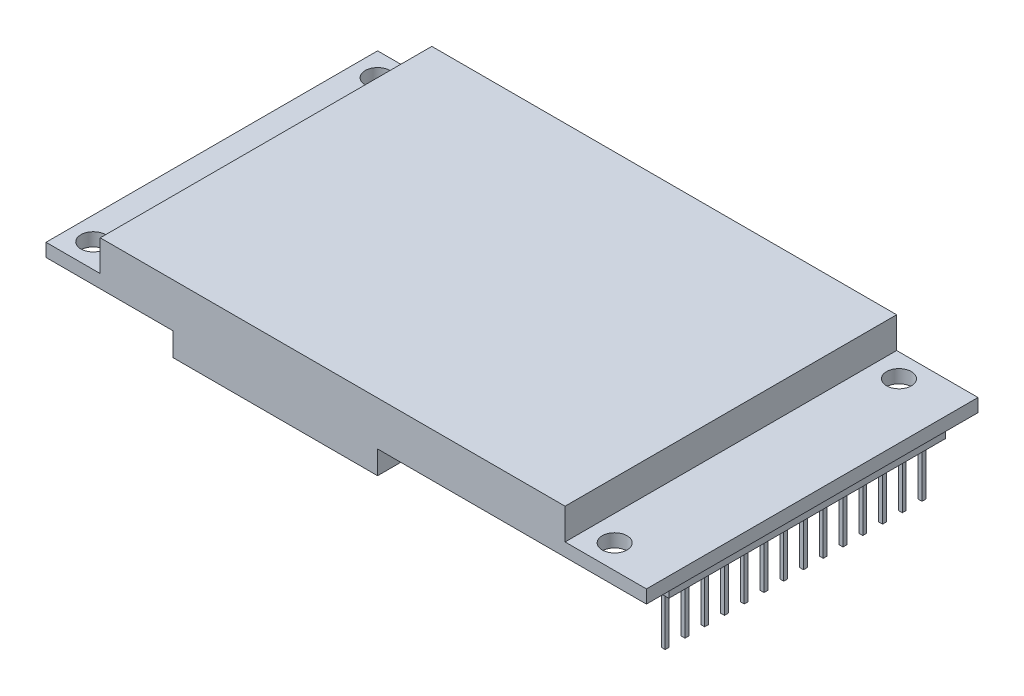
SolidWorks part; units mm, degrees
ref_plane "Płaszczyzna przednia" through (0, 0, 0) normal (0, 0, 1) x (1, 0, 0)
ref_plane "Płaszczyzna górna" through (0, 0, 0) normal (0, 1, 0) x (1, 0, 0)
ref_plane "Płaszczyzna prawa" through (0, 0, 0) normal (1, 0, 0) x (0, 0, -1)
sketch "Szkic1" plane through (0, 0, 0) normal (0, 1, 0) x (1, 0, 0)
  line L1 (-38.75, -21.4) -> (38.75, -21.4)
  line L2 (-38.75, -21.4) -> (-38.75, 21.4)
  line L3 (-38.75, 21.4) -> (38.75, 21.4)
  line L4 (38.75, -21.4) -> (38.75, 21.4)
  line L5 (-38.75, -21.4) -> (38.75, 21.4) construction
  line L6 (-38.75, 21.4) -> (38.75, -21.4) construction
  circle A0 centre (-35.75, 18.4) radius 1.6
  circle A2 centre (31.55, 18.4) radius 1.6
  circle A3 centre (31.55, -18.3) radius 1.6
  circle A4 centre (-35.75, -18.3) radius 1.6
  point P0 (0, 0)
  point P8 (0, 0)
  point P9 (0, 0)
  point P10 (0, 0)
  dimension "D3" = 3.2
  dimension "D8" = 36.7
  dimension "D10" = 67.3
  dimension "D1" = 42.8
  dimension "D2" = 77.5
  dimension "D6" = 3
  dimension "D7" = 3
  dimension "D4" = 2
  dimension "D5" = 2
extrude "Dodanie-wyciągnięcie1" add sketch "Szkic1" along normal blind 1.7
sketch "Szkic2" plane through (0, 1.7, 0) normal (0, 1, 0) x (1, 0, 0)
  line L0 (-38.75, -21.4) -> (38.75, -21.4) construction
  line L1 (-31.75, -21.4) -> (28.25, -21.4)
  line L2 (-31.75, -21.4) -> (-31.75, 21.4)
  line L3 (-31.75, 21.4) -> (28.25, 21.4)
  line L4 (28.25, -21.4) -> (28.25, 21.4)
  line L5 (38.75, 21.4) -> (-38.75, 21.4) construction
  line L6 (-38.75, 21.4) -> (-38.75, -21.4) construction
  dimension "D1" = 60
  dimension "D2" = 7
extrude "Dodanie-wyciągnięcie2" add sketch "Szkic2" along normal blind 4
sketch "Szkic3" plane through (0, 0, 0) normal (0, -1, 0) x (1, 0, 0)
  line L0 (4.05, 21.4) -> (4.05, 4.5)
  line L1 (-38.75, 21.4) -> (38.75, 21.4) construction
  line L2 (4.05, 4.5) -> (-20.45, 4.5)
  line L3 (-20.45, 4.5) -> (-20.45, 9.5)
  line L4 (-20.45, 9.5) -> (-22.35, 12.4)
  line L5 (-22.35, 12.4) -> (-22.35, 21.4)
  line L6 (-22.35, 21.4) -> (4.05, 21.4)
  line L7 (-38.75, -21.4) -> (-38.75, 21.4) construction
  point P2 (0, 0)
  dimension "D1" = 16.9
  dimension "D2" = 26.4
  dimension "D3" = 24.5
  dimension "D4" = 5
  dimension "D5" = 9
  dimension "D6" = 16.4
extrude "Dodanie-wyciągnięcie3" add sketch "Szkic3" along normal blind 3
sketch "Szkic4" plane through (0, 0, 0) normal (0, -1, 0) x (1, 0, 0)
  line L0 (38.75, 21.4) -> (38.75, -21.4) construction
  line L1 (34.55, -17.9) -> (38.05, -17.9)
  line L2 (34.55, -17.9) -> (34.55, 17.8)
  line L3 (34.55, 17.8) -> (38.05, 17.8)
  line L4 (38.05, -17.9) -> (38.05, 17.8)
  line L5 (38.75, -21.4) -> (-38.75, -21.4) construction
  dimension "D1" = 35.7
  dimension "D2" = 3.5
  dimension "D3" = 0.7
  dimension "D4" = 3.5
extrude "Dodanie-wyciągnięcie4" add sketch "Szkic4" along normal blind 8.5
sketch "Szkic5" plane through (0, -8.5, 0) normal (0, -1, 0) x (1, 0, 0)
  line L0 (36.3, 17.8) -> (36.3, -17.9) construction
  line L1 (36.05, 16.775) -> (36.55, 16.775)
  line L2 (36.05, 16.775) -> (36.05, 16.275)
  line L3 (36.05, 16.275) -> (36.55, 16.275)
  line L4 (36.55, 16.775) -> (36.55, 16.275)
  line L5 (38.05, 17.8) -> (34.55, 17.8) construction
  line L6 (34.55, -17.9) -> (38.05, -17.9) construction
  line L7 (36.55, 14.225) -> (36.55, 13.725)
  line L8 (36.05, 13.725) -> (36.55, 13.725)
  line L9 (36.05, 14.225) -> (36.05, 13.725)
  line L10 (36.05, 14.225) -> (36.55, 14.225)
  line L11 (36.55, 11.675) -> (36.55, 11.175)
  line L12 (36.05, 11.175) -> (36.55, 11.175)
  line L13 (36.05, 11.675) -> (36.05, 11.175)
  line L14 (36.05, 11.675) -> (36.55, 11.675)
  line L15 (36.55, 9.125) -> (36.55, 8.625)
  line L16 (36.05, 8.625) -> (36.55, 8.625)
  line L17 (36.05, 9.125) -> (36.05, 8.625)
  line L18 (36.05, 9.125) -> (36.55, 9.125)
  line L19 (36.55, 6.575) -> (36.55, 6.075)
  line L20 (36.05, 6.075) -> (36.55, 6.075)
  line L21 (36.05, 6.575) -> (36.05, 6.075)
  line L22 (36.05, 6.575) -> (36.55, 6.575)
  line L23 (36.55, 4.025) -> (36.55, 3.525)
  line L24 (36.05, 3.525) -> (36.55, 3.525)
  line L25 (36.05, 4.025) -> (36.05, 3.525)
  line L26 (36.05, 4.025) -> (36.55, 4.025)
  line L27 (36.55, 1.475) -> (36.55, 0.975)
  line L28 (36.05, 0.975) -> (36.55, 0.975)
  line L29 (36.05, 1.475) -> (36.05, 0.975)
  line L30 (36.05, 1.475) -> (36.55, 1.475)
  line L31 (36.55, -1.075) -> (36.55, -1.575)
  line L32 (36.05, -1.575) -> (36.55, -1.575)
  line L33 (36.05, -1.075) -> (36.05, -1.575)
  line L34 (36.05, -1.075) -> (36.55, -1.075)
  line L35 (36.55, -3.625) -> (36.55, -4.125)
  line L36 (36.05, -4.125) -> (36.55, -4.125)
  line L37 (36.05, -3.625) -> (36.05, -4.125)
  line L38 (36.05, -3.625) -> (36.55, -3.625)
  line L39 (36.55, -6.175) -> (36.55, -6.675)
  line L40 (36.05, -6.675) -> (36.55, -6.675)
  line L41 (36.05, -6.175) -> (36.05, -6.675)
  line L42 (36.05, -6.175) -> (36.55, -6.175)
  line L43 (36.55, -8.725) -> (36.55, -9.225)
  line L44 (36.05, -9.225) -> (36.55, -9.225)
  line L45 (36.05, -8.725) -> (36.05, -9.225)
  line L46 (36.05, -8.725) -> (36.55, -8.725)
  line L47 (36.55, -11.275) -> (36.55, -11.775)
  line L48 (36.05, -11.775) -> (36.55, -11.775)
  line L49 (36.05, -11.275) -> (36.05, -11.775)
  line L50 (36.05, -11.275) -> (36.55, -11.275)
  line L51 (36.55, -13.825) -> (36.55, -14.325)
  line L52 (36.05, -14.325) -> (36.55, -14.325)
  line L53 (36.05, -13.825) -> (36.05, -14.325)
  line L54 (36.05, -13.825) -> (36.55, -13.825)
  line L55 (36.55, -16.375) -> (36.55, -16.875)
  line L56 (36.05, -16.875) -> (36.55, -16.875)
  line L57 (36.05, -16.375) -> (36.05, -16.875)
  line L58 (36.05, -16.375) -> (36.55, -16.375)
  line L59 (34.55, -17.9) -> (38.05, -17.9) construction
  line L61 (29.053, 28.2127) -> (49.6422, 28.2127)
  line L62 (29.053, 28.2127) -> (29.053, -31.0519)
  line L63 (29.053, -31.0519) -> (49.6422, -31.0519)
  line L64 (49.6422, 28.2127) -> (49.6422, -31.0519)
  point P10 (36.3, 16.775)
  dimension "D1" = 0.5
  dimension "D3" = 1.025
  dimension "D4" = 1.025
  dimension "D5" = 2.05
  dimension "D2" = 14
extrude "Wytnij-wyciągnięcie1" cut sketch "Szkic5" against normal blind 7
equation "\"D5@Szkic5\"=\"D4@Szkic5\"*2"
